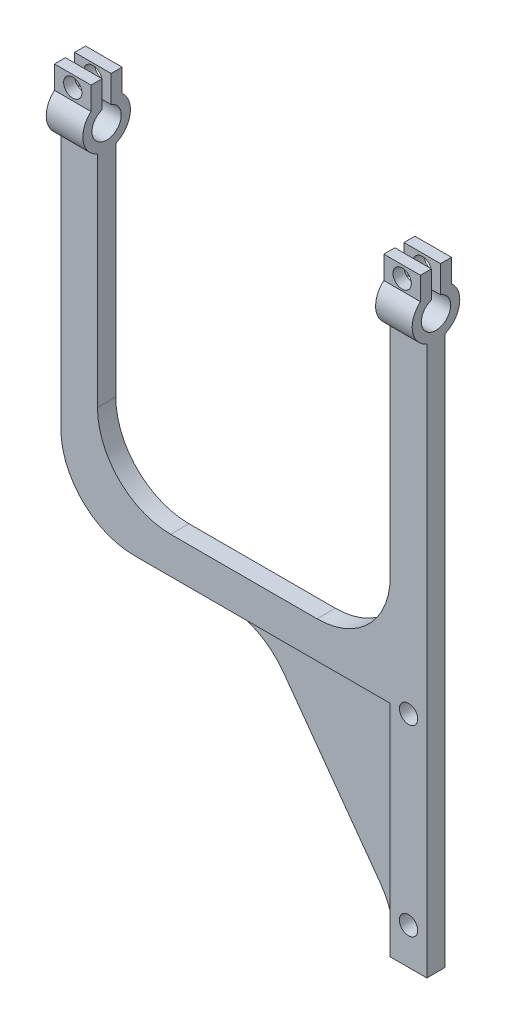
SolidWorks part; units mm, degrees
material "Alloy Steel"
ref_plane "Front Plane" through (0, 0, 0) normal (0, 0, 1) x (1, 0, 0)
ref_plane "Top Plane" through (0, 0, 0) normal (0, 1, 0) x (1, 0, 0)
ref_plane "Right Plane" through (0, 0, 0) normal (1, 0, 0) x (0, 0, -1)
sketch "Sketch1" plane through (0, 0, 0) normal (0, 0, 1) x (1, 0, 0)
  line L0 (-16.4029, -2.1583) -> (-6.4029, -2.1583) construction
  line L1 (-16.4029, 32.8417) -> (-6.4029, 32.8417)
  line L2 (-16.4029, 32.8417) -> (-16.4029, -37.1583)
  line L3 (-16.4029, -37.1583) -> (-6.4029, -37.1583)
  line L4 (-6.4029, 32.8417) -> (-6.4029, -37.1583)
  circle A0 centre (-11.4029, 22.8417) radius 2.5
  circle A1 centre (-11.4029, -27.1583) radius 2.5
  dimension "D3" = 5
  dimension "D1" = 10
  dimension "D2" = 70
  dimension "D4" = 10
  dimension "D5" = 5
extrude "Boss-Extrude1" add sketch "Sketch1" along normal blind 5
sketch "Sketch2" plane through (-16.4029, 0, 0) normal (-1, 0, 0) x (0, 0, 1)
  line L0 (0, 32.8417) -> (5, 32.8417)
  line L1 (0, 32.8417) -> (0, 22.8417)
  line L2 (5, 32.8417) -> (5, 22.8417)
  line L3 (0, 22.8417) -> (5, 22.8417)
  dimension "D1" = 10
extrude "Boss-Extrude2" add sketch "Sketch2" along normal blind 90
sketch "Sketch3" plane through (0, 0, 0) normal (0, 0, -1) x (-1, 0, 0)
  line L0 (16.4029, -27.1583) -> (52.5513, 22.8417)
  line L1 (16.4029, 22.8417) -> (16.4029, -37.1583) construction
  line L2 (106.4029, 22.8417) -> (16.4029, 22.8417) construction
  line L3 (16.4029, -27.1583) -> (16.4029, 22.8417)
  line L4 (16.4029, 22.8417) -> (52.5513, 22.8417)
extrude "Boss-Extrude3" add sketch "Sketch3" against normal blind 4
sketch "Sketch4" plane through (0, 0, 0) normal (0, 0, -1) x (-1, 0, 0)
sketch "Sketch5" plane through (0, 32.8417, 0) normal (0, 1, 0) x (1, 0, 0)
  line L0 (-6.4029, 0) -> (-6.4029, -5)
  line L1 (-6.4029, 0) -> (-16.4029, 0)
  line L2 (-6.4029, -5) -> (-16.4029, -5)
  line L3 (-16.4029, 0) -> (-16.4029, -5)
  line L4 (-6.4029, -5) -> (-106.4029, -5) construction
  line L5 (-106.4029, 0) -> (-96.4029, 0)
  line L6 (-106.4029, 0) -> (-106.4029, -5)
  line L7 (-106.4029, -5) -> (-96.4029, -5)
  line L8 (-96.4029, 0) -> (-96.4029, -5)
  dimension "D1" = 10
  dimension "D2" = 10
extrude "Boss-Extrude4" add sketch "Sketch5" along normal blind 80
sketch "Sketch6" plane through (-6.4029, 0, 0) normal (1, 0, 0) x (0, 0, -1)
  line L0 (-5, 112.8417) -> (0, 112.8417) construction
  line L1 (-6.75, 123.7598) -> (-6.75, 130.0098)
  line L2 (-6.75, 130.0098) -> (-3.75, 130.0098)
  line L3 (-3.75, 130.0098) -> (-3.75, 122.6414)
  line L4 (-2.5, 118.8417) -> (-2.5, 125.3417) construction
  line L5 (1.75, 130.0098) -> (-1.25, 130.0098)
  line L6 (1.75, 123.7598) -> (1.75, 130.0098)
  line L7 (-1.25, 130.0098) -> (-1.25, 122.6414)
  circle A0 centre (-2.5, 118.8417) radius 6.5
  circle A1 centre (-2.5, 118.8417) radius 4
  point P7 (-2.5, 112.8417)
  line M8 (0, 112.8417) -> (-5, 112.8417)
  dimension "D1" = 13
  dimension "D2" = 8
  dimension "D3" = 3
  dimension "D4" = 6.25
  dimension "D5" = 1.25
extrude "Boss-Extrude5" add sketch "Sketch6" against normal blind 10 contours A0 L3 L2 L1 | A1 L3 A0 L7 M8 | A0 L6 L5 L7
sketch "Sketch7" plane through (0, 0, -1.75) normal (0, 0, -1) x (-1, 0, 0)
  line L0 (16.4029, 130.0098) -> (6.4029, 130.0098) construction
  circle A0 centre (11.4029, 126.7362) radius 2.5
  point P6 (11.4029, 130.0098)
  dimension "D1" = 5
extrude "Cut-Extrude1" cut sketch "Sketch7" against normal blind 10
sketch "Sketch8" plane through (-106.4029, 0, 0) normal (-1, 0, 0) x (0, 0, 1)
  line L0 (0, 112.8417) -> (5, 112.8417) construction
  line L1 (-1.75, 130.0098) -> (-1.75, 123.7598)
  line L2 (-1.75, 130.0098) -> (1.25, 130.0098)
  line L3 (1.25, 130.0098) -> (1.25, 122.6414)
  line L4 (2.5, 118.8417) -> (2.5, 122.8417) construction
  line L5 (6.75, 130.0098) -> (6.75, 123.7598)
  line L6 (6.75, 130.0098) -> (3.75, 130.0098)
  line L7 (3.75, 130.0098) -> (3.75, 122.6414)
  circle A0 centre (2.5, 118.8417) radius 6.5
  circle A1 centre (2.5, 118.8417) radius 4
  point P7 (2.5, 112.8417)
  line M6 (5, 112.8417) -> (0, 112.8417)
  dimension "D1" = 13
  dimension "D2" = 8
  dimension "D3" = 2.5
  dimension "D4" = 3
  dimension "D5" = 6.25
extrude "Boss-Extrude6" add sketch "Sketch8" against normal blind 10 contours A1 L3 A0 L7 M6 | A0 L3 L2 L1 | A0 L5 L6 L7
sketch "Sketch9" plane through (0, 0, 6.75) normal (0, 0, 1) x (1, 0, 0)
  line L0 (-96.4029, 130.0098) -> (-106.4029, 130.0098) construction
  circle A0 centre (-101.4029, 126.9218) radius 2.5
  point P5 (-101.4029, 130.0098)
  dimension "D1" = 5
extrude "Cut-Extrude2" cut sketch "Sketch9" against normal blind 10
sketch "Sketch10" plane through (0, 0, 0) normal (0, 0, -1) x (-1, 0, 0)
  line L0 (16.4029, -27.1583) -> (52.5513, 22.8417)
  line L1 (52.5513, 22.8417) -> (16.4029, 22.8417)
  line L2 (16.4029, 22.8417) -> (16.4029, -27.1583)
extrude "Cut-Extrude3" cut sketch "Sketch10" against normal blind 1 contours L2 L0 L1
fillet "Fillet1" radius 20 5 edges at (-16.4029, -27.1583, 2.5) (-52.5513, 22.8417, 2.5) (-106.4029, 22.8417, 2.5) (-16.4029, 32.8417, 2.5) (-96.4029, 32.8417, 2.5)
